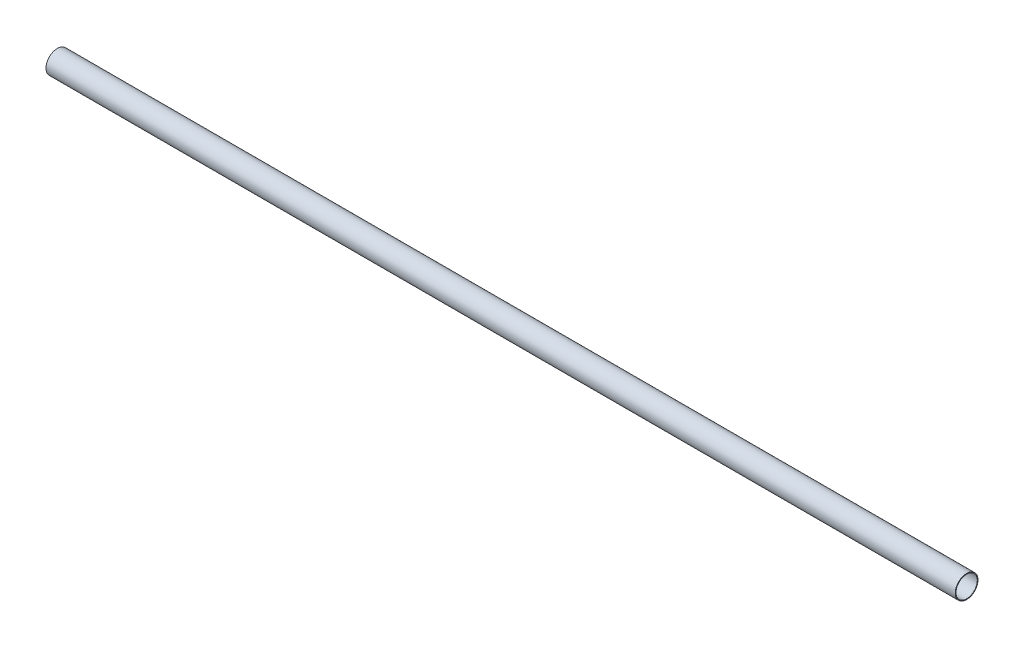
SolidWorks part; units mm, degrees
ref_plane "Спереди" through (0, 0, 0) normal (0, 0, 1) x (1, 0, 0)
ref_plane "Сверху" through (0, 0, 0) normal (0, 1, 0) x (1, 0, 0)
ref_plane "Справа" through (0, 0, 0) normal (1, 0, 0) x (0, 0, -1)
sketch "Эскиз1" plane through (0, 0, 0) normal (1, 0, 0) x (0, 0, -1)
  circle A0 centre (0, 0) radius 25
  circle A1 centre (0, 0) radius 23.45
  dimension "D1" = 50
  dimension "D2" = 46.9
extrude "Бобышка-Вытянуть1" add sketch "Эскиз1" along normal blind 2000
